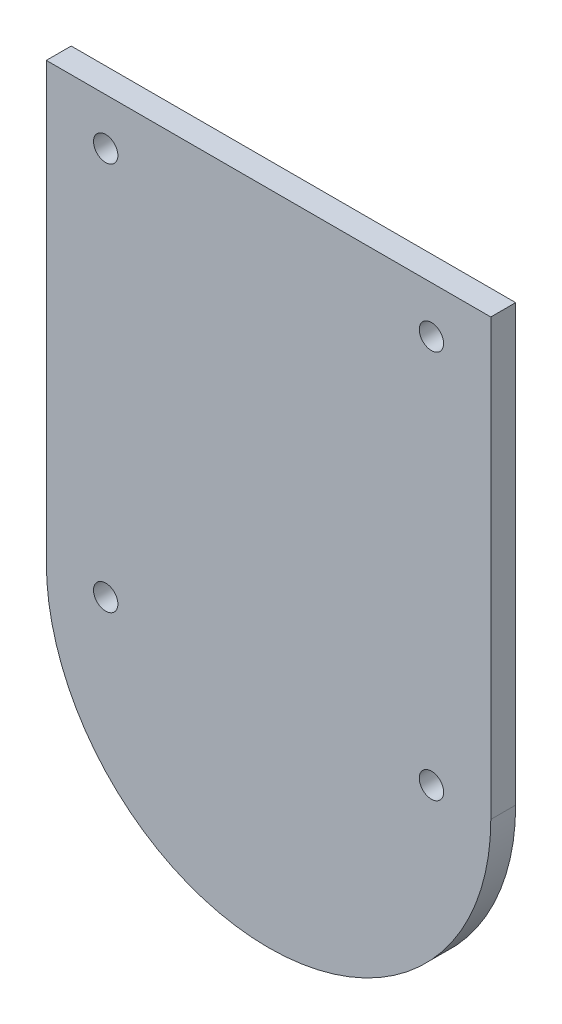
SolidWorks part; units mm, degrees
ref_plane "前视基准面" through (0, 0, 0) normal (0, 0, 1) x (1, 0, 0)
ref_plane "上视基准面" through (0, 0, 0) normal (0, 1, 0) x (1, 0, 0)
ref_plane "右视基准面" through (0, 0, 0) normal (1, 0, 0) x (0, 0, -1)
sketch "Model" plane through (0, 0, 0) normal (0, 0, 1) x (1, 0, 0)
  line L0 (-37.2121, 27.6698) -> (-8.6121, 27.6698)
  line L1 (-37.2121, 31.6698) -> (-8.6121, 31.6698)
  line L2 (-28.9121, 54.6698) -> (-37.2121, 31.6698)
  line L3 (-16.9121, 54.6698) -> (-8.6121, 31.6698)
  line L4 (-28.9121, 54.6698) -> (-16.9121, 54.6698)
  line L5 (-37.2121, 27.6698) -> (-8.6121, 27.6698)
  line L6 (-28.8921, 24.6698) -> (-16.9321, 24.6698)
  line L7 (-30.3921, -0.3302) -> (-30.3921, 23.1698)
  line L8 (-15.4321, -0.3302) -> (-15.4321, 23.1698)
  line L9 (-28.1621, 24.6698) -> (-28.1621, 27.6698)
  line L10 (-17.6621, 24.6698) -> (-17.6621, 27.6698)
  line L11 (-8.6121, 27.6698) -> (-8.6121, -0.3302)
  line L12 (-8.6121, 31.6698) -> (-8.6121, -0.3302)
  line L13 (-37.2121, 27.6698) -> (-37.2121, -0.3302)
  line L14 (-37.2121, 31.6698) -> (-37.2121, -0.3302)
  line L15 (-28.1621, 27.6698) -> (-28.1621, 31.6698)
  line L16 (-17.6621, 27.6698) -> (-17.6621, 31.6698)
  circle A0 centre (-22.9121, -0.3302) radius 6.5
  arc A1 (-15.4321, 23.1698) -> (-16.9321, 24.6698) centre (-16.9321, 23.1698) ccw
  arc A2 (-28.8921, 24.6698) -> (-30.3921, 23.1698) centre (-28.8921, 23.1698) ccw
  arc A3 (-37.2121, -0.3302) -> (-8.6121, -0.3302) centre (-22.9121, -0.3302) ccw
  arc A4 (-30.3921, -0.3302) -> (-15.4321, -0.3302) centre (-22.9121, -0.3302) ccw
  circle A5 centre (-12.4321, -0.3302) radius 0.7835
  circle A6 centre (-33.3921, -0.3302) radius 0.7835
  circle A7 centre (-12.4321, 24.6698) radius 0.7835
  circle A8 centre (-33.3921, 24.6698) radius 0.7835
  circle A9 centre (-33.2121, 29.6698) radius 1.2294
  circle A10 centre (-22.9121, 29.6698) radius 1.2294
  circle A11 centre (-12.6121, 29.6698) radius 1.2294
  circle A12 centre (-22.9121, 49.6698) radius 1.2294
extrude "凸台-拉伸8" add sketch "Model" along normal blind 1.6 contours A4 L7 A2 L6 L9 L0 L13 A3 L11 L10 A1 L8 A8 A7 A6 A5 | L7 A4 L8 A1 L6 A2 A0 | L6 L10 L5 L9 | L5 L16 L1 L15 A10 | A10 | A0
sketch "草图1" plane through (0, 0, 1.6) normal (0, 0, 1) x (1, 0, 0)
  line L0 (-28.1621, 27.6698) -> (-17.6621, 27.6698)
  line L1 (-17.6621, 27.6698) -> (-17.6621, 34.986)
  line L2 (-17.6621, 34.986) -> (-28.7435, 34.986)
  line L3 (-28.7435, 34.986) -> (-28.1621, 27.6698)
extrude "切除-拉伸1" cut sketch "草图1" against normal blind 10
